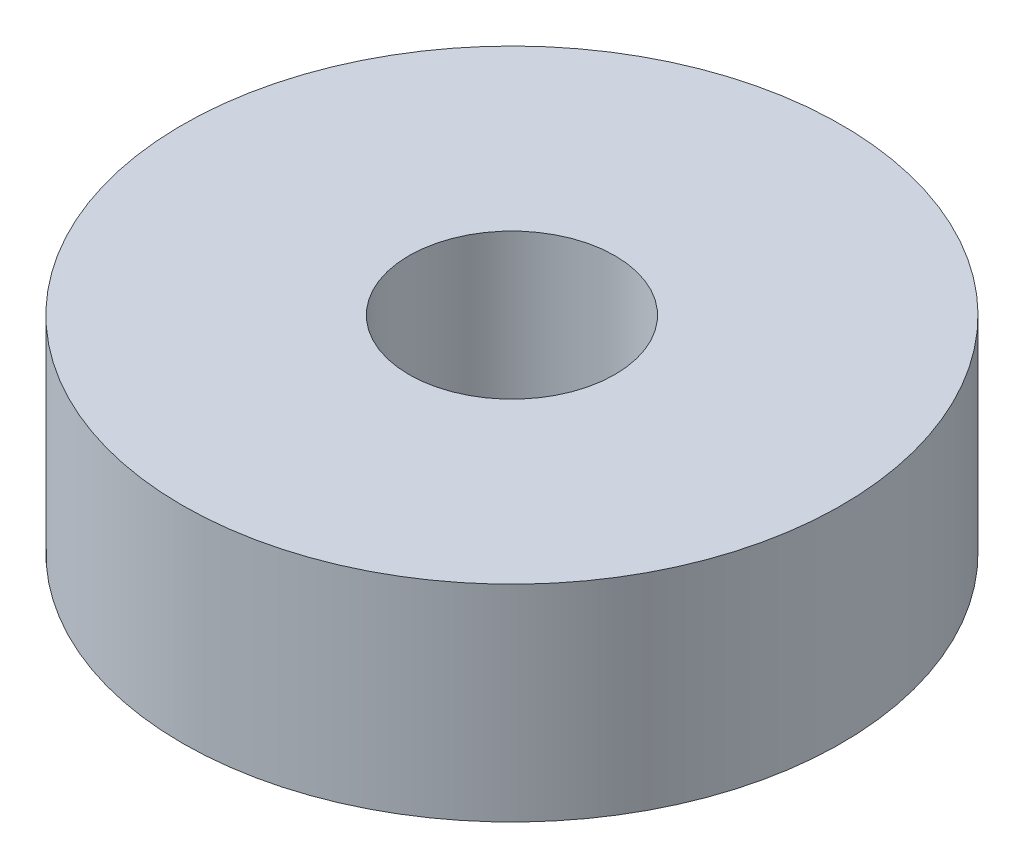
SolidWorks part; units mm, degrees
material "Alloy Steel"
ref_plane "Front Plane" through (0, 0, 0) normal (0, 0, 1) x (1, 0, 0)
ref_plane "Top Plane" through (0, 0, 0) normal (0, 1, 0) x (1, 0, 0)
ref_plane "Right Plane" through (0, 0, 0) normal (1, 0, 0) x (0, 0, -1)
sketch "Sketch1" plane through (0, 0, 0) normal (0, 1, 0) x (1, 0, 0)
  circle A0 centre (0, 0) radius 8
  circle A1 centre (0, 0) radius 2.5
  dimension "D1" = 5
  dimension "D2" = 16
extrude "Boss-Extrude1" add sketch "Sketch1" along normal blind 5
